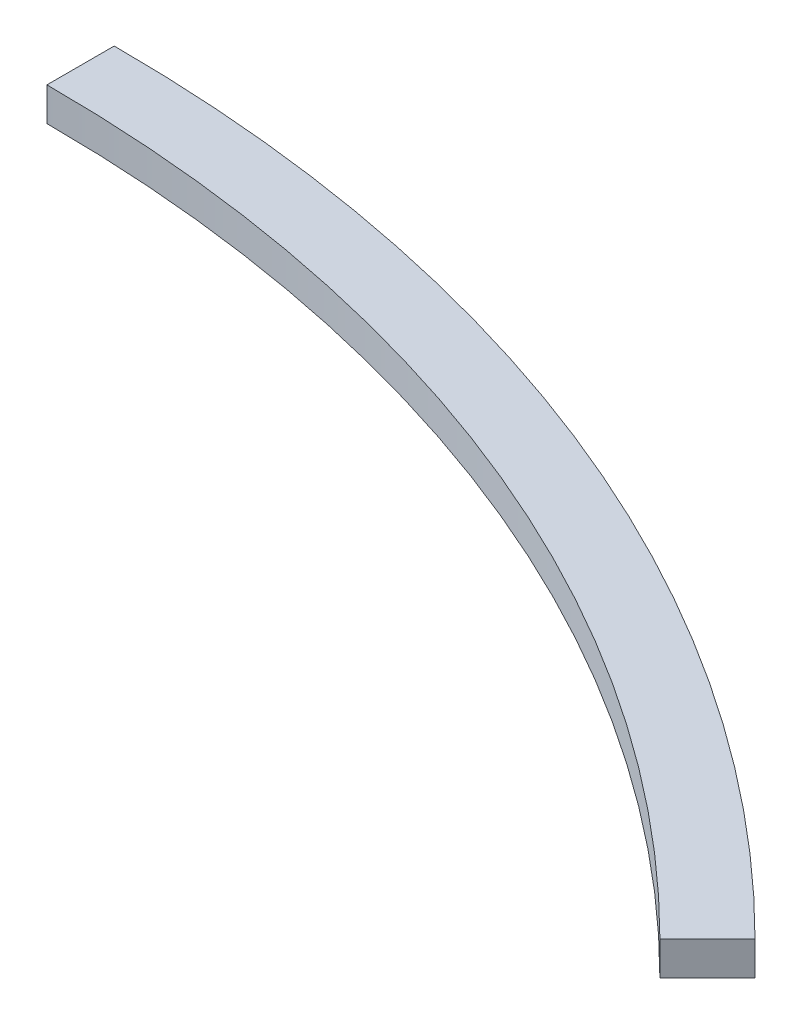
SolidWorks part; units mm, degrees
ref_plane "Front Plane" through (0, 0, 0) normal (0, 0, 1) x (1, 0, 0)
ref_plane "Top Plane" through (0, 0, 0) normal (0, 1, 0) x (1, 0, 0)
ref_plane "Right Plane" through (0, 0, 0) normal (1, 0, 0) x (0, 0, -1)
sketch "Sketch1" plane through (0, 0, 0) normal (0, 1, 0) x (1, 0, 0)
  line L0 (0, 0) -> (0, 440) construction
  line L1 (0, 0) -> (325.2691, 325.2691) construction
  line L2 (0, 440) -> (0, 460)
  line L3 (311.127, 311.127) -> (325.2691, 325.2691)
  arc A0 (0, 440) -> (311.127, 311.127) centre (0, 0) cw
  arc A1 (0, 460) -> (325.2691, 325.2691) centre (0, 0) cw
  dimension "D1" = 20
  dimension "D2" = 460
  dimension "D3" = 440
  dimension "D4" = 45
extrude "Boss-Extrude1" add sketch "Sketch1" along normal blind 10 contours A1 L2 A0 L3
